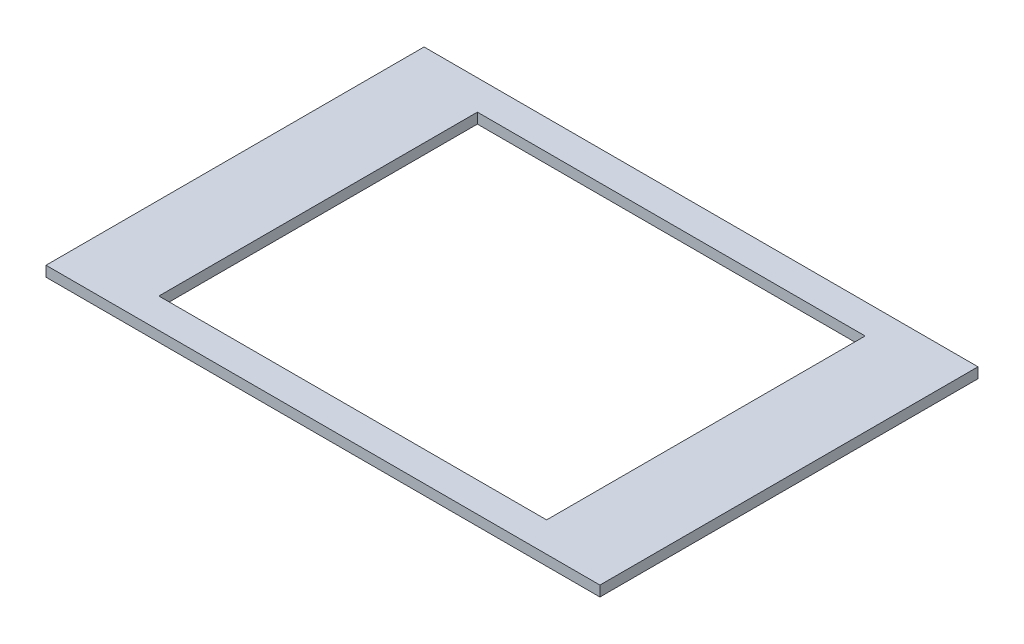
SolidWorks part; units mm, degrees
ref_plane "Front Plane" through (0, 0, 0) normal (0, 0, 1) x (1, 0, 0)
ref_plane "Top Plane" through (0, 0, 0) normal (0, 1, 0) x (1, 0, 0)
ref_plane "Right Plane" through (0, 0, 0) normal (1, 0, 0) x (0, 0, -1)
sketch "Sketch1" plane through (0, 0, 0) normal (0, 1, 0) x (1, 0, 0)
  line L1 (127, 86.6775) -> (-127, 86.6775)
  line L2 (127, 86.6775) -> (127, -86.6775)
  line L3 (127, -86.6775) -> (-127, -86.6775)
  line L4 (-127, 86.6775) -> (-127, -86.6775)
  line L5 (127, 86.6775) -> (-127, -86.6775) construction
  line L6 (127, -86.6775) -> (-127, 86.6775) construction
  line L7 (88.9, 73.025) -> (-88.9, 73.025)
  line L8 (88.9, 73.025) -> (88.9, -73.025)
  line L9 (88.9, -73.025) -> (-88.9, -73.025)
  line L10 (-88.9, 73.025) -> (-88.9, -73.025)
  line L11 (88.9, 73.025) -> (-88.9, -73.025) construction
  line L12 (88.9, -73.025) -> (-88.9, 73.025) construction
  point P0 (0, 0)
  point P6 (0, 0)
  dimension "D1" = 173.355
  dimension "D2" = 254
  dimension "D3" = 146.05
  dimension "D4" = 177.8
extrude "Boss-Extrude1" add sketch "Sketch1" along normal blind 4.7625
